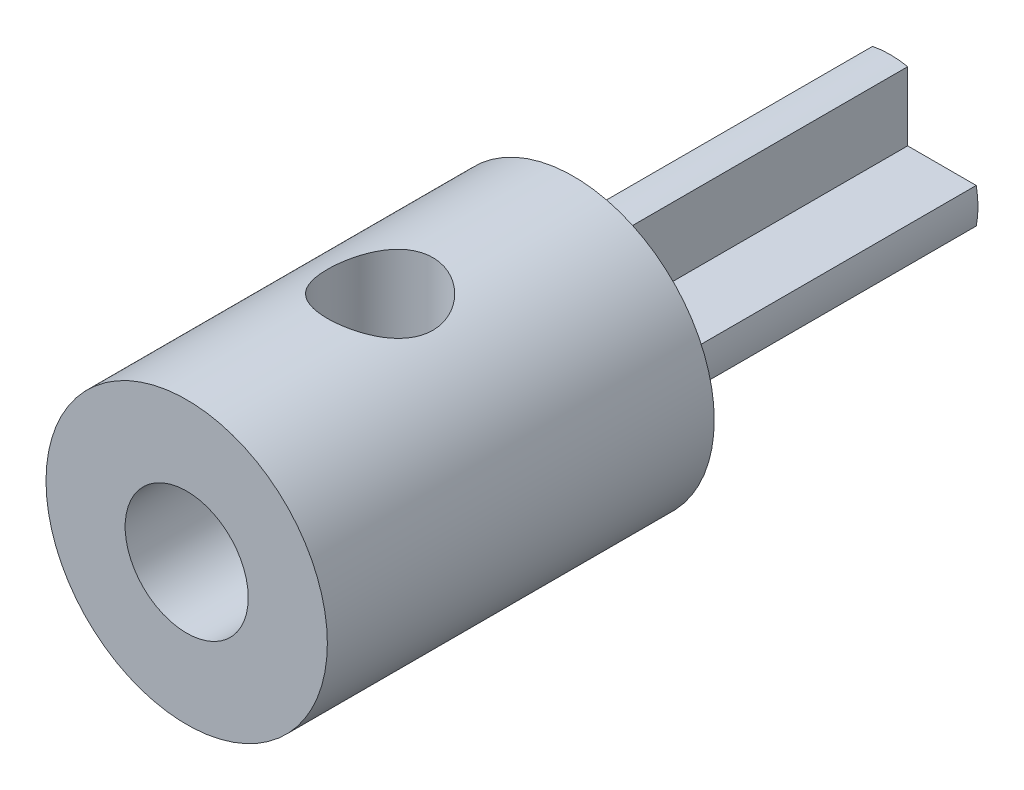
SolidWorks part; units mm, degrees
ref_plane "Front Plane" through (0, 0, 0) normal (0, 0, 1) x (1, 0, 0)
ref_plane "Top Plane" through (0, 0, 0) normal (0, 1, 0) x (1, 0, 0)
ref_plane "Right Plane" through (0, 0, 0) normal (1, 0, 0) x (0, 0, -1)
sketch "Sketch1" plane through (0, 0, 0) normal (0, 0, 1) x (1, 0, 0)
  circle A0 centre (0, 0) radius 4
  circle A1 centre (0, 0) radius 1.75
  dimension "D1" = 8
  dimension "D2" = 3.5
extrude "Boss-Extrude1" add sketch "Sketch1" along normal blind 10
sketch "Sketch2" plane through (0, 0, 0) normal (0, 0, -1) x (-1, 0, 0)
  line L0 (0, 2.5) -> (0, -1.75) construction
  line L1 (-2.5, 0) -> (2.5, 0) construction
  line L2 (-0.5, 2.4495) -> (-0.5, -2.4495)
  line L3 (0.5, 2.4495) -> (0.5, -2.4495)
  line L4 (2.4495, 0.5) -> (-2.4495, 0.5)
  line L5 (2.4495, -0.5) -> (-2.4495, -0.5)
  circle A0 centre (0, 0) radius 4
  circle A1 centre (0, 0) radius 2.5
  circle A2 centre (0, 0) radius 1.75 construction
  point P16 (0.5, 0)
  point P17 (-0.5, 0)
  point P22 (0, -0.5)
  point P23 (0, 0.5)
  circle M8 centre (0, 0) radius 1.75
  dimension "D1" = 5
  dimension "D2" = 0.5
  dimension "D3" = 0.5
extrude "Boss-Extrude2" add sketch "Sketch2" along normal blind 10 contours L4 L3 L2 M8 | L3 A1 L2 M8 | L5 L2 L4 M8 | L4 A1 L5 M8 | L2 A1 L3 M8 | L3 L5 L2 M8 | L5 L3 L4 L2 | L5 L4 L3 M8 | L5 A1 L4 M8
sketch "Sketch3" plane through (0, 0, 0) normal (0, 0, -1) x (-1, 0, 0)
  circle A0 centre (0, 0) radius 4
extrude "Boss-Extrude3" add sketch "Sketch3" along normal blind 1
sketch "Sketch4" plane through (0, 0, 0) normal (0, 1, 0) x (1, 0, 0)
  line L0 (-4, -4.5) -> (4, -4.5) construction
  line L1 (-4, 1) -> (-4, -10) construction
  line L2 (4, -10) -> (4, 1) construction
  line L3 (0, 1) -> (0, -10) construction
  line L4 (0.5, 1) -> (-0.5, 1) construction
  line L5 (-4, -10) -> (4, -10) construction
  circle A0 centre (0, -4.5) radius 1.5
  dimension "D1" = 3
extrude "Cut-Extrude1" cut sketch "Sketch4" against normal through all and the other way through all
